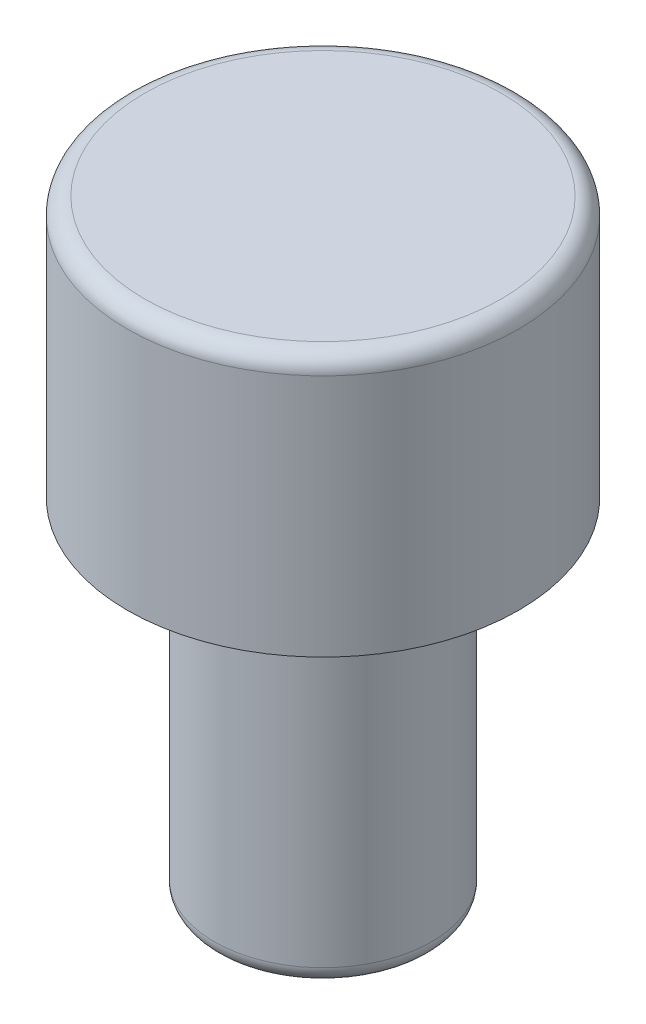
SolidWorks part; units mm, degrees
ref_plane "Front Plane" through (0, 0, 0) normal (0, 0, 1) x (1, 0, 0)
ref_plane "Top Plane" through (0, 0, 0) normal (0, 1, 0) x (1, 0, 0)
ref_plane "Right Plane" through (0, 0, 0) normal (1, 0, 0) x (0, 0, -1)
sketch "Sketch1" plane through (0, 0, 0) normal (0, 0, 1) x (1, 0, 0)
  line L1 (0, 0) -> (2.25, 0)
  line L2 (0, 0) -> (0, 3)
  line L3 (0, 3) -> (2.25, 3)
  line L4 (2.25, 0) -> (2.25, 3)
  line L5 (0, 0) -> (1.25, 0)
  line L6 (0, 0) -> (0, -4)
  line L7 (0, -4) -> (1.25, -4)
  line L8 (1.25, 0) -> (1.25, -4)
  dimension "D1" = 3
  dimension "D2" = 4
  dimension "D3" = 1.25
  dimension "D4" = 2.25
revolve "Revolve1" add sketch "Sketch1" angle 360 about L6
fillet "Fillet1" radius 0.2 1 edges at (-2.25, 3, 0)
fillet "Fillet2" radius 0.2 1 edges at (-1.25, -4, 0)
